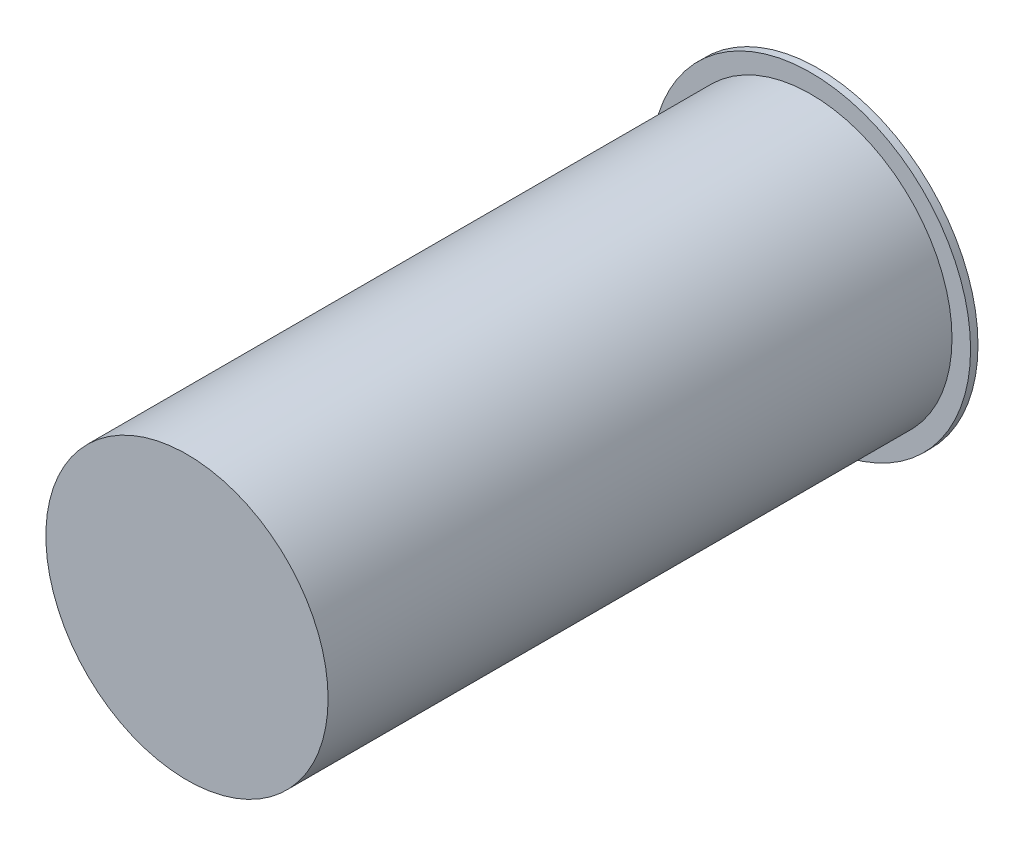
SolidWorks part; units mm, degrees
material "AISI Type 316L stainless steel"
ref_plane "Front Plane" through (0, 0, 0) normal (0, 0, 1) x (1, 0, 0)
ref_plane "Top Plane" through (0, 0, 0) normal (0, 1, 0) x (1, 0, 0)
ref_plane "Right Plane" through (0, 0, 0) normal (1, 0, 0) x (0, 0, -1)
sketch "Sketch1" plane through (0, 0, 0) normal (0, 1, 0) x (1, 0, 0)
  line L0 (0, 0) -> (0, 31.2828) construction
  line L1 (0, 2) -> (0, -42)
  line L2 (0, -42) -> (9.5, -42)
  line L3 (9.5, -42) -> (9.5, 0)
  line L4 (9.5, 0) -> (10.75, 0)
  line L5 (10.75, 0) -> (10.75, 0.5)
  line L6 (10.75, 0.5) -> (8, 2)
  line L7 (8, 2) -> (0, 2)
  dimension "D1" = 19
  dimension "D2" = 21.5
  dimension "D3" = 2
  dimension "D4" = 0.5
  dimension "D5" = 16
  dimension "D6" = 42
revolve "Revolve1" add sketch "Sketch1" angle 360 about L0
